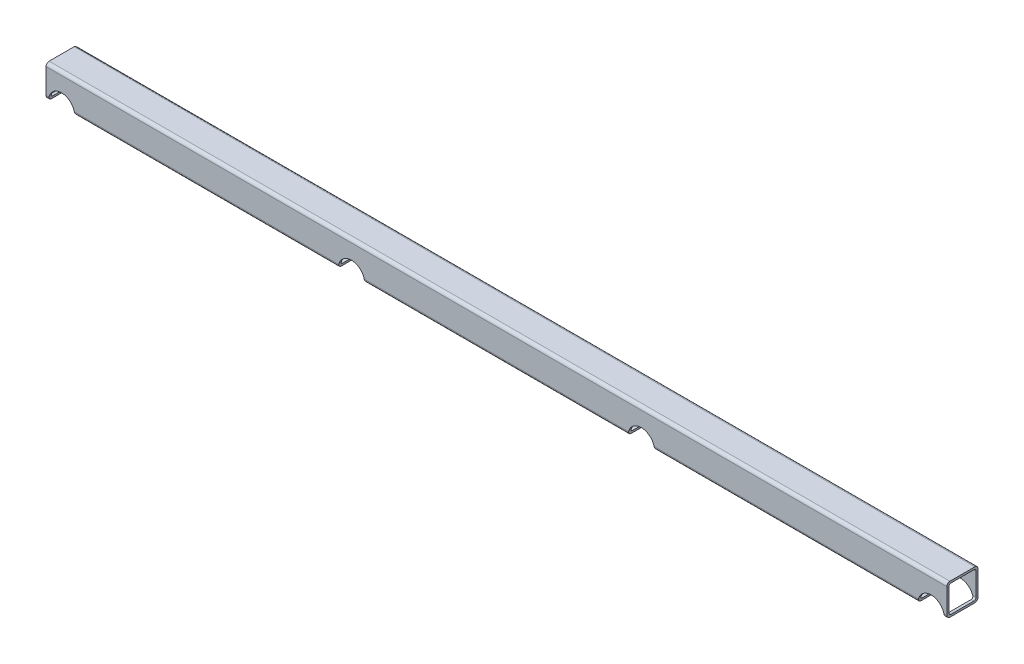
SolidWorks part; units mm, degrees
material "AISI 1020"
ref_plane "Спереди" through (0, 0, 0) normal (0, 0, 1) x (1, 0, 0)
ref_plane "Сверху" through (0, 0, 0) normal (0, 1, 0) x (1, 0, 0)
ref_plane "Справа" through (0, 0, 0) normal (1, 0, 0) x (0, 0, -1)
sketch "Эскиз2" plane through (0, 0, 0) normal (1, 0, 0) x (0, 0, -1)
  point P0 (0, 0)
  line B0 (-12, 30) -> (12, 30)
  line B1 (-15, 27) -> (-15, 3)
  line B2 (-12, 0) -> (12, 0)
  line B3 (15, 27) -> (15, 3)
  line B4 (-11, 28) -> (11, 28)
  line B5 (-13, 26) -> (-13, 4)
  line B6 (-11, 2) -> (11, 2)
  line B7 (13, 26) -> (13, 4)
  arc B8 (-15, 3) -> (-12, 0) centre (-12, 3) ccw
  arc B9 (12, 0) -> (15, 3) centre (12, 3) ccw
  arc B10 (12, 30) -> (15, 27) centre (12, 27) cw
  arc B11 (-12, 30) -> (-15, 27) centre (-12, 27) ccw
  arc B12 (-13, 4) -> (-11, 2) centre (-11, 4) ccw
  arc B13 (11, 2) -> (13, 4) centre (11, 4) ccw
  arc B14 (11, 28) -> (13, 26) centre (11, 26) cw
  arc B15 (-11, 28) -> (-13, 26) centre (-11, 26) ccw
sketch_block_instance "Блок-30х30х2-1"
sketch_block "Блок-30х30х2" parameters "D3"=3, "D4"=2, "D1"=30, "D2"=2
ref_plane "Плоскость1" through (835.4709, 0, 0) normal (1, 0, 0) x (0, 0, -1)
extrude "Бобышка-Вытянуть1" add sketch "Эскиз2" against normal blind 15 and the other way offset from surface (850.4709 mm away) 15 other way up to plane "Плоскость1"
sketch "Эскиз3" plane through (0, 0, 15) normal (0, 0, 1) x (1, 0, 0)
  line L0 (835.4709, -50) -> (835.4709, 50) construction
  line L1 (835.4709, 0) -> (980.4709, 145) construction
  circle A0 centre (0, 0) radius 12.6
  circle A1 centre (278.4903, 0) radius 12.6
  circle A2 centre (556.9806, 0) radius 12.6
  circle A3 centre (835.4709, 0) radius 12.6
  dimension "D1" = 25.2
extrude "Вырез-Вытянуть1" cut sketch "Эскиз3" against normal through all
